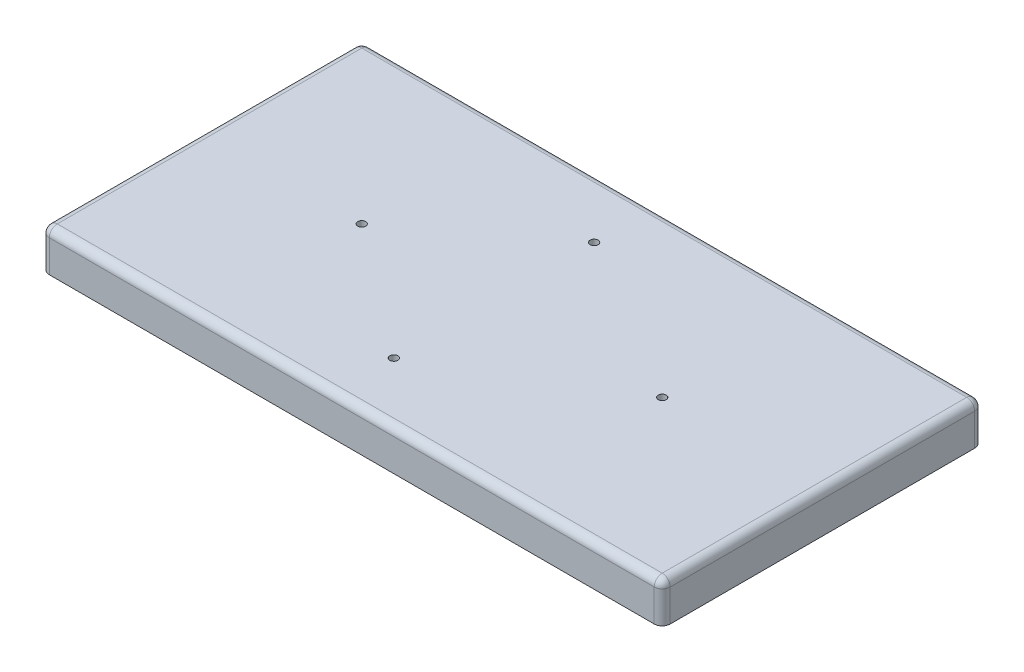
SolidWorks part; units mm, degrees
material "PVC 0.007 Plasticized"
ref_plane "Front Plane" through (0, 0, 0) normal (0, 0, 1) x (1, 0, 0)
ref_plane "Top Plane" through (0, 0, 0) normal (0, 1, 0) x (1, 0, 0)
ref_plane "Right Plane" through (0, 0, 0) normal (1, 0, 0) x (0, 0, -1)
sketch "Sketch2" plane through (0, 0, 0) normal (0, 1, 0) x (1, 0, 0)
  line L1 (0, 0) -> (155, 0)
  line L2 (0, 0) -> (0, 80)
  line L3 (0, 80) -> (155, 80)
  line L4 (155, 0) -> (155, 80)
  circle A0 centre (40, 40) radius 1
  circle A1 centre (115, 40) radius 1
  circle A2 centre (73, 65) radius 1
  circle A3 centre (73, 15) radius 1
  point P13 (0, 0)
  dimension "D3" = 2
  dimension "D6" = 2
  dimension "D9" = 2
  dimension "D10" = 2
  dimension "D1" = 155
  dimension "D2" = 80
  dimension "D4" = 40
  dimension "D5" = 40
  dimension "D7" = 40
  dimension "D8" = 40
  dimension "D11" = 73
  dimension "D12" = 73
  dimension "D13" = 15
  dimension "D14" = 15
extrude "Boss-Extrude1" add sketch "Sketch2" against normal blind 5
sketch "Sketch3" plane through (0, 0, 0) normal (0, 1, 0) x (1, 0, 0)
  line L1 (0, 80) -> (155, 80)
  line L2 (0, 80) -> (0, 0)
  line L3 (0, 0) -> (155, 0)
  line L4 (155, 80) -> (155, 0)
  line L5 (3, 77) -> (152, 77)
  line L6 (3, 77) -> (3, 3)
  line L7 (3, 3) -> (152, 3)
  line L8 (152, 77) -> (152, 3)
  dimension "D1" = 3
  dimension "D2" = 3
  dimension "D3" = 3
  dimension "D4" = 3
extrude "Boss-Extrude2" add sketch "Sketch3" against normal blind 10
sketch "Sketch4" plane through (0, 0, 0) normal (0, 1, 0) x (1, 0, 0)
  line L1 (0, 80) -> (155, 80)
  line L2 (0, 80) -> (0, 0)
  line L3 (0, 0) -> (155, 0)
  line L4 (155, 80) -> (155, 0)
  line L5 (5, 75) -> (150, 75)
  line L6 (5, 75) -> (5, 5)
  line L7 (5, 5) -> (150, 5)
  line L8 (150, 75) -> (150, 5)
  dimension "D1" = 5
  dimension "D2" = 5
  dimension "D3" = 5
  dimension "D4" = 5
extrude "Boss-Extrude3" add sketch "Sketch4" against normal blind 7
fillet "Fillet1" radius 2 8 edges at (155, 0, -40) (77.5, 0, -80) (0, 0, -40) (77.5, 0, 0) (155, -5, 0) (155, -5, -80) (0, -5, -80) (0, -5, 0)
